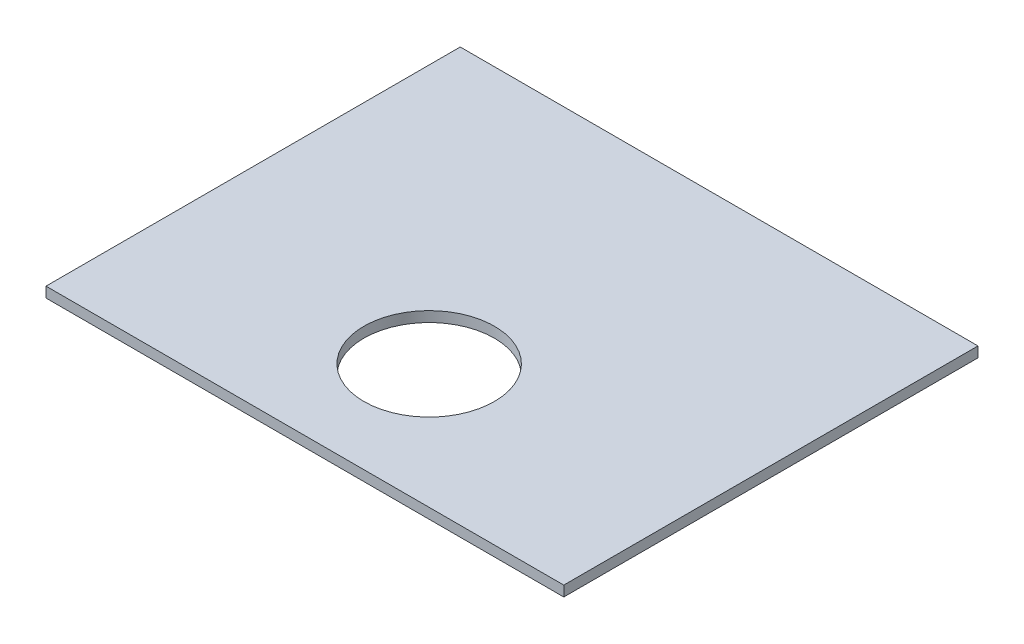
SolidWorks part; units mm, degrees
ref_plane "Ön Düzlem" through (0, 0, 0) normal (0, 0, 1) x (1, 0, 0)
ref_plane "Üst Düzlem" through (0, 0, 0) normal (0, 1, 0) x (1, 0, 0)
ref_plane "Sağ Düzlem" through (0, 0, 0) normal (1, 0, 0) x (0, 0, -1)
sketch "Sketch1" plane through (0, 0, 0) normal (0, 1, 0) x (1, 0, 0)
  line L1 (-250, 200) -> (250, 200)
  line L2 (-250, 200) -> (-250, -200)
  line L3 (-250, -200) -> (250, -200)
  line L4 (250, 200) -> (250, -200)
  line L5 (-250, 200) -> (250, -200) construction
  line L6 (-250, -200) -> (250, 200) construction
  point P0 (0, 0)
  dimension "D1" = 500
  dimension "D2" = 400
extrude "Boss-Extrude1" add sketch "Sketch1" against normal blind 10 contours L2 L3 L4 L1
sketch "Sketch2" plane through (0, 0, 0) normal (0, 1, 0) x (1, 0, 0)
  line L1 (-250, 200) -> (250, 200) construction
  circle A0 centre (0, -80) radius 63
  dimension "D1" = 280
extrude "Cut-Extrude1" cut sketch "Sketch2" against normal blind 20
